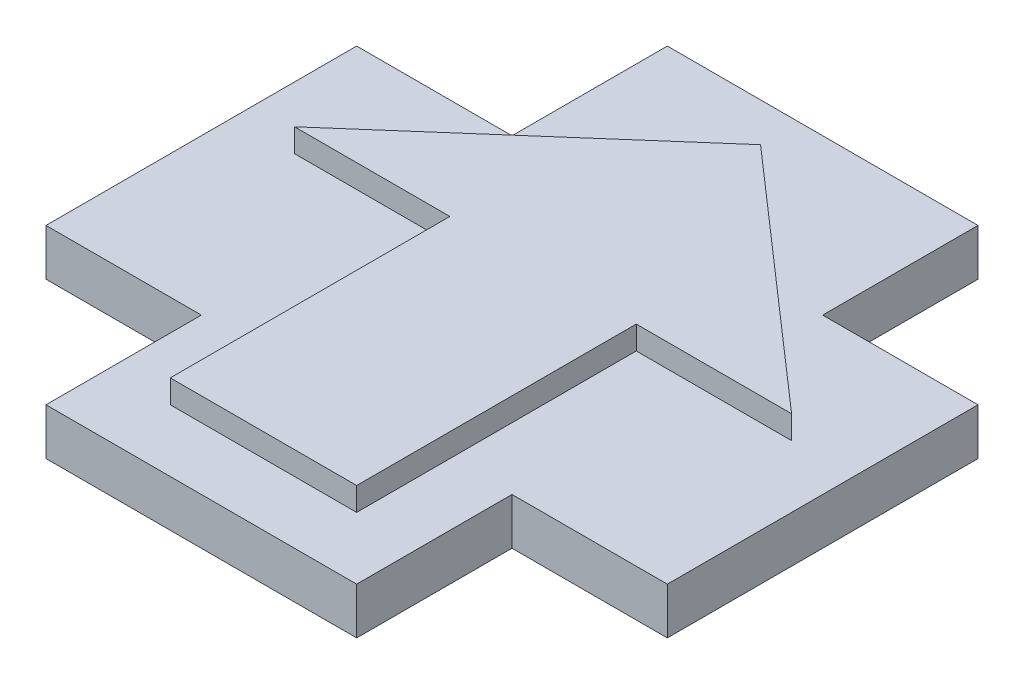
SolidWorks part; units mm, degrees
ref_plane "Front Plane" through (0, 0, 0) normal (0, 0, 1) x (1, 0, 0)
ref_plane "Top Plane" through (0, 0, 0) normal (0, 1, 0) x (1, 0, 0)
ref_plane "Right Plane" through (0, 0, 0) normal (1, 0, 0) x (0, 0, -1)
sketch "Sketch1" plane through (0, 0, 0) normal (0, 1, 0) x (1, 0, 0)
  line L0 (-8, 8) -> (-8, 1) construction
  line L5 (8, -8) -> (-8, -8) construction
  line L6 (8, -8) -> (8, 8) construction
  line L7 (8, 8) -> (-8, 8) construction
  line L8 (-8, -8) -> (-8, 8) construction
  line L9 (-8, 1) -> (-3, 1)
  line L10 (8, 1) -> (0, 8)
  line L11 (0, 8) -> (-8, 1)
  line L12 (3, 1) -> (8, 1)
  line L13 (3, -8) -> (-3, -8)
  line L14 (3, -8) -> (3, 1)
  line L16 (-3, -8) -> (-3, 1)
  line L17 (-8, 0) -> (8, 0) construction
  line L19 (10, -10) -> (-10, -10) construction
  line L20 (10, -10) -> (10, 10) construction
  line L21 (10, 10) -> (-10, 10) construction
  line L22 (-10, -10) -> (-10, 10) construction
  line L23 (0, 10) -> (0, -10) construction
  line L24 (10, 0) -> (-10, 0) construction
  line L25 (10, 5) -> (-10, 5)
  line L26 (10, 5) -> (10, -5)
  line L27 (10, -5) -> (-10, -5)
  line L28 (-10, 5) -> (-10, -5)
  line L29 (0, -5) -> (0, 5) construction
  line L30 (10, 0) -> (-10, 0) construction
  line L31 (5, -10) -> (-5, -10)
  line L32 (5, -10) -> (5, 10)
  line L33 (5, 10) -> (-5, 10)
  line L34 (-5, -10) -> (-5, 10)
  line L35 (0, 10) -> (0, -10) construction
  line L36 (5, 0) -> (-5, 0) construction
  point P0 (0, 0)
  point P1 (0, 0)
  point P4 (0, 0)
  point P15 (0, 0)
  point P19 (0, 0)
  point P23 (0, 0)
  dimension "D1" = 20
  dimension "D2" = 20
  dimension "D3" = 16
  dimension "D4" = 16
  dimension "D5" = 7
  dimension "D6" = 6
  dimension "D7" = 5
  dimension "D8" = 10
  dimension "D9" = 10
extrude "Boss-Extrude2" add sketch "Sketch1" along normal blind 3 contours L34 L9 L16 L27 L14 L12 L32 L10 L25 L11 | L14 L27 L16 L13 | L9 L34 L11 | L25 L10 L11 | L32 L12 L10
ref_plane "Plane1" through (0, 1.5, 0) normal (0, 1, 0) x (1, 0, 0)
sketch "Sketch4" plane through (0, 1.5, 0) normal (0, 1, 0) x (1, 0, 0)
  line L4 (10, 5) -> (-10, 5)
  line L5 (10, -5) -> (10, 5)
  line L6 (-10, -5) -> (10, -5)
  line L7 (-8, 1) -> (-3, 1)
  line L8 (-3, 1) -> (-3, -8)
  line L9 (-3, -8) -> (3, -8)
  line L10 (3, -8) -> (3, 1)
  line L11 (3, 1) -> (8, 1)
  line L12 (8, 1) -> (0, 8)
  line L13 (0, 8) -> (-8, 1)
  line L14 (-8, 1) -> (-3, 1)
  line L15 (-3, 1) -> (-3, -8)
  line L16 (-3, -8) -> (3, -8)
  line L17 (3, -8) -> (3, 1)
  line L18 (3, 1) -> (8, 1)
  line L19 (8, 1) -> (0, 8)
  line L20 (0, 8) -> (-8, 1)
  line L21 (-10, 5) -> (-10, -5)
  line L22 (10, 5) -> (-10, 5)
  line L23 (10, -5) -> (10, 5)
  line L24 (-10, -5) -> (10, -5)
  line L25 (-10, 5) -> (-10, -5)
  line L26 (-5, -10) -> (5, -10)
  line L27 (5, -10) -> (5, 10)
  line L28 (5, 10) -> (-5, 10)
  line L29 (-5, 10) -> (-5, -10)
  line L30 (-5, -10) -> (5, -10)
  line L31 (5, -10) -> (5, 10)
  line L32 (5, 10) -> (-5, 10)
  line L33 (-5, 10) -> (-5, -10)
  dimension "D1" = 0
  dimension "D2" = 0
  dimension "D3" = 0
extrude "Boss-Extrude3" add sketch "Sketch4" along normal blind 0.75 and the other way blind 0.75 contours L31 L24 L23 L22 L19 L18 | L24 L31 L18 L17 | L32 L33 L22 L20 L19 L31 | L33 L22 L25 L24 L14 L20 | L22 L33 L20 | L19 L31 L22 | L14 L33 L24 L15 | L24 L33 L30 L31 L17 L16 L15
